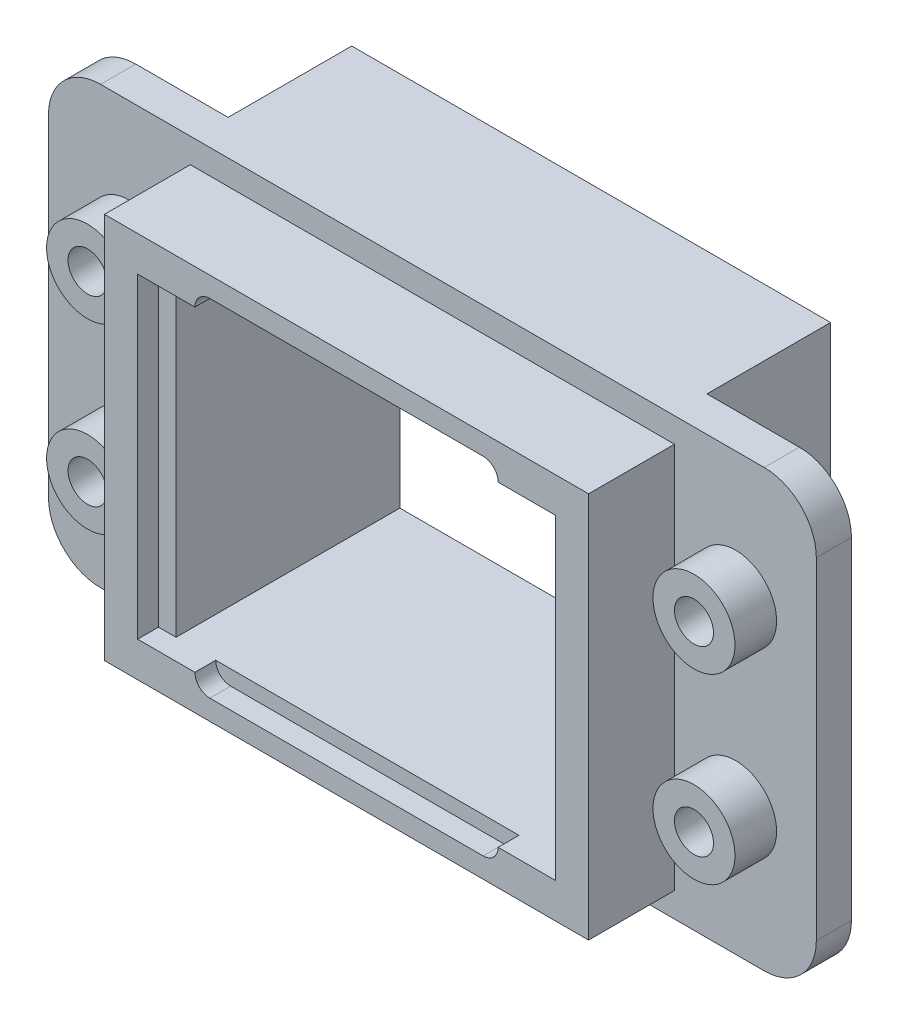
SolidWorks part; units mm, degrees
ref_plane "Спереди" through (0, 0, 0) normal (0, 0, 1) x (1, 0, 0)
ref_plane "Сверху" through (0, 0, 0) normal (0, 1, 0) x (1, 0, 0)
ref_plane "Справа" through (0, 0, 0) normal (1, 0, 0) x (0, 0, -1)
sketch "Эскиз1" plane through (0, 0, 0) normal (0, 0, 1) x (1, 0, 0)
  line L1 (-12.75, -8.375) -> (12.75, -8.375)
  line L2 (-14.75, -6.375) -> (-14.75, 6.375)
  line L3 (-12.75, 8.375) -> (12.75, 8.375)
  line L4 (14.75, -6.375) -> (14.75, 6.375)
  line L5 (-14.75, -8.375) -> (14.75, 8.375) construction
  line L6 (-14.75, 8.375) -> (14.75, -8.375) construction
  arc A0 (-12.75, -8.375) -> (-14.75, -6.375) centre (-12.75, -6.375) cw
  arc A1 (12.75, -8.375) -> (14.75, -6.375) centre (12.75, -6.375) ccw
  arc A2 (12.75, 8.375) -> (14.75, 6.375) centre (12.75, 6.375) cw
  arc A3 (-14.75, 6.375) -> (-12.75, 8.375) centre (-12.75, 6.375) cw
  point P0 (0, 0)
  dimension "D3" = 2
  dimension "D1" = 29.5
  dimension "D2" = 16.75
extrude "Бобышка-Вытянуть1" add sketch "Эскиз1" along normal blind 1.35
sketch "Эскиз8" plane through (0, 0, 0) normal (0, 0, -1) x (-1, 0, 0)
  line L0 (12.75, -8.375) -> (-12.75, -8.375) construction
  line L1 (9.2, 8.375) -> (-9.2, 8.375)
  line L2 (9.2, 8.375) -> (9.2, -8.375)
  line L3 (9.2, -8.375) -> (-9.2, -8.375)
  line L4 (-9.2, 8.375) -> (-9.2, -8.375)
  line L5 (9.2, 8.375) -> (-9.2, -8.375) construction
  line L6 (9.2, -8.375) -> (-9.2, 8.375) construction
  point P0 (0, 0)
  dimension "D1" = 18.4
extrude "Бобышка-Вытянуть4" add sketch "Эскиз8" along normal blind 4.75
sketch "Эскиз2" plane through (0, 0, 1.35) normal (0, 0, 1) x (1, 0, 0)
  line L0 (0, 0) -> (0, 9.8387) construction
  line L1 (0, 0) -> (9.7136, 0) construction
  circle A0 centre (-11.65, 3.5) radius 1.575
  circle A1 centre (11.65, 3.5) radius 1.575
  circle A2 centre (11.65, -3.5) radius 1.575
  circle A3 centre (-11.65, -3.5) radius 1.575
  dimension "D1" = 3.15
  dimension "D2" = 7
  dimension "D3" = 23.3
extrude "Бобышка-Вытянуть2" add sketch "Эскиз2" along normal blind 1.6
sketch "Эскиз4" plane through (0, 0, 1.35) normal (0, 0, 1) x (1, 0, 0)
  line L1 (-9.3, -7.425) -> (9.3, -7.425)
  line L2 (-9.3, -7.425) -> (-9.3, 7.425)
  line L3 (-9.3, 7.425) -> (9.3, 7.425)
  line L4 (9.3, -7.425) -> (9.3, 7.425)
  line L5 (-9.3, -7.425) -> (9.3, 7.425) construction
  line L6 (-9.3, 7.425) -> (9.3, -7.425) construction
  point P0 (0, 0)
  dimension "D1" = 18.6
  dimension "D2" = 14.85
extrude "Бобышка-Вытянуть3" add sketch "Эскиз4" along normal blind 3.3
sketch "Эскиз3" plane through (0, 0, 4.65) normal (0, 0, 1) x (1, 0, 0)
  line L1 (-7.35, -6.075) -> (7.35, -6.075)
  line L2 (-7.35, -6.075) -> (-7.35, 6.075)
  line L3 (-7.35, 6.075) -> (7.35, 6.075)
  line L4 (7.35, -6.075) -> (7.35, 6.075)
  line L5 (-7.35, -6.075) -> (7.35, 6.075) construction
  line L6 (-7.35, 6.075) -> (7.35, -6.075) construction
  point P0 (0, 0)
  dimension "D1" = 14.7
  dimension "D2" = 12.15
extrude "Вырез-Вытянуть1" cut sketch "Эскиз3" against normal through all
sketch "Эскиз5" plane through (0, 0, 4.65) normal (0, 0, 1) x (1, 0, 0)
  line L0 (-5.25, 6.075) -> (5.25, 6.075) construction
  line L1 (7.35, 6.075) -> (-7.35, 6.075) construction
  line L2 (-5.25, 6.65) -> (5.25, 6.65)
  line L3 (-5.25, 5.5) -> (5.25, 5.5)
  line L4 (0, 0) -> (17.0697, 0) construction
  line L5 (-5.25, -6.075) -> (5.25, -6.075) construction
  line L6 (-5.25, -6.65) -> (5.25, -6.65)
  line L7 (-5.25, -5.5) -> (5.25, -5.5)
  line L8 (-7.35, 6.075) -> (-7.35, -6.075) construction
  line L9 (-8.025, 6.075) -> (-7.35, 6.075)
  line L10 (-8.025, 6.075) -> (-8.025, -6.075)
  line L11 (-8.025, -6.075) -> (-7.35, -6.075)
  line L12 (-7.35, 6.075) -> (-7.35, -6.075)
  line L13 (7.35, 6.075) -> (8.025, 6.075)
  line L14 (7.35, 6.075) -> (7.35, -6.075)
  line L15 (7.35, -6.075) -> (8.025, -6.075)
  line L16 (8.025, 6.075) -> (8.025, -6.075)
  line L17 (7.35, -6.075) -> (7.35, 6.075) construction
  arc A0 (-5.25, 6.65) -> (-5.25, 5.5) centre (-5.25, 6.075) ccw
  arc A1 (5.25, 5.5) -> (5.25, 6.65) centre (5.25, 6.075) ccw
  arc A2 (-5.25, -6.65) -> (-5.25, -5.5) centre (-5.25, -6.075) cw
  arc A3 (5.25, -5.5) -> (5.25, -6.65) centre (5.25, -6.075) cw
  point P4 (0, 6.075)
  point P14 (0, -6.075)
  dimension "D1" = 13.3
  dimension "D2" = 10.5
  dimension "D3" = 16.05
extrude "Вырез-Вытянуть2" cut sketch "Эскиз5" against normal blind 0.8
sketch "Эскиз6" plane through (0, 0, 2.95) normal (0, 0, 1) x (1, 0, 0)
  circle A0 centre (-11.65, 3.5) radius 0.75
  circle A1 centre (-11.65, -3.5) radius 0.75
  circle A2 centre (11.65, 3.5) radius 0.75
  circle A3 centre (11.65, -3.5) radius 0.75
  dimension "D1" = 1.5
extrude "Вырез-Вытянуть3" cut sketch "Эскиз6" against normal through all
